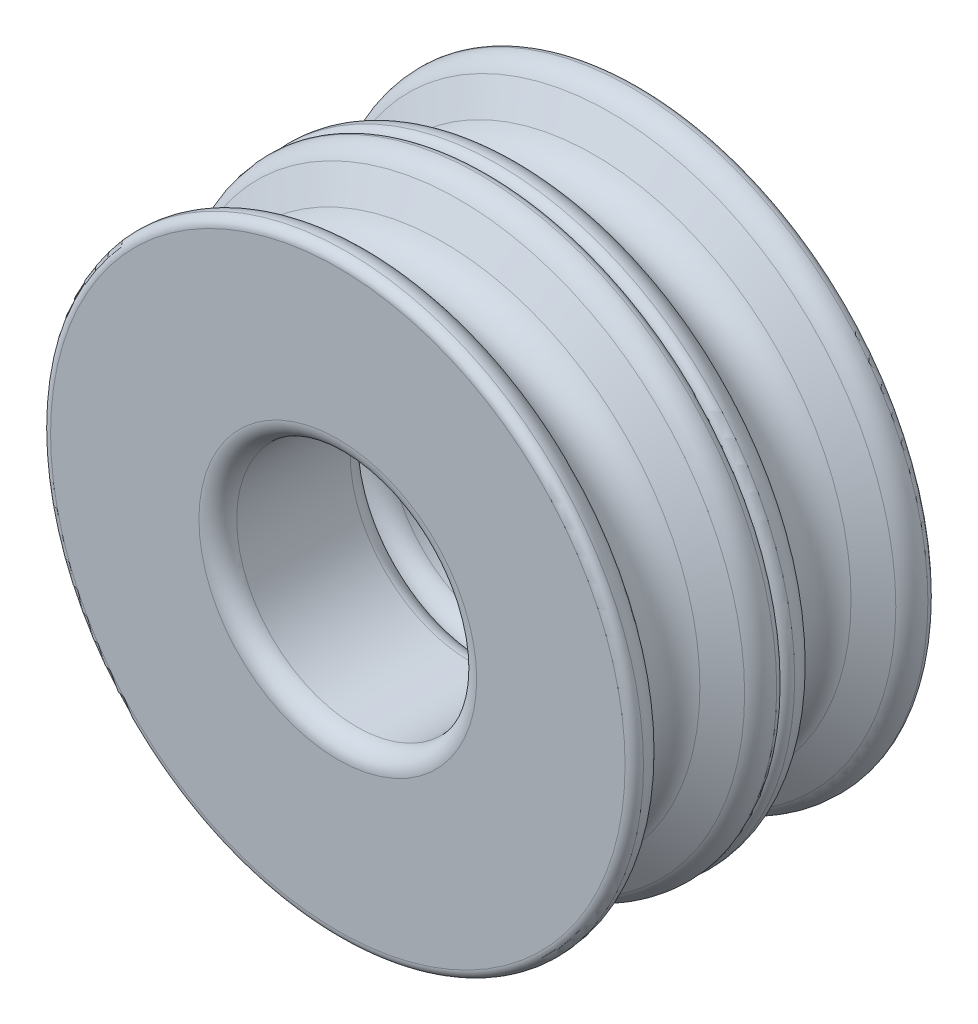
SolidWorks part; units mm, degrees
ref_plane "Front Plane" through (0, 0, 0) normal (0, 0, 1) x (1, 0, 0)
ref_plane "Top Plane" through (0, 0, 0) normal (0, 1, 0) x (1, 0, 0)
ref_plane "Right Plane" through (0, 0, 0) normal (1, 0, 0) x (0, 0, -1)
sketch "Sketch1" plane through (0, 0, 0) normal (1, 0, 0) x (0, 0, -1)
  line L0 (0, 0) -> (0, 17451.5356) construction
  line L2 (-4, 0) -> (-4, 15.2006)
  line L3 (4, 0) -> (4, 15.2006)
  line L6 (-2.4257, 15.1015) -> (-1.5588, 13.6)
  line L7 (2.4257, 15.1015) -> (1.5588, 13.6)
  line L9 (0, 0) -> (-50000, 0) construction
  line L10 (-4, 0) -> (4, 0)
  arc A0 (-4, 15.2006) -> (-3.525, 15.7) centre (-3.5, 15.2006) cw
  arc A1 (4, 15.2006) -> (3.525, 15.7) centre (3.5, 15.2006) ccw
  arc A2 (-3.525, 15.7) -> (-2.4257, 15.1015) centre (-3.465, 14.5015) cw
  arc A3 (3.525, 15.7) -> (2.4257, 15.1015) centre (3.465, 14.5015) ccw
  arc A4 (-1.5588, 13.6) -> (1.5588, 13.6) centre (0, 14.5) ccw
  point P4 (0, 0)
  point P6 (0, 0)
  point P18 (0, 12.7)
  point P20 (0, 0)
  point P21 (-4, 0)
  point P25 (0, 0)
  dimension "D2" = 0.5
  dimension "D4" = 1.2
  dimension "D5" = 1.8
  dimension "D1" = 8
  dimension "D6" = 3
  dimension "D7" = 60
  dimension "D8" = 12.7
revolve "Revolve1" add sketch "Sketch1" angle 360 about L9
sketch "Sketch4" plane through (0, 0, -4) normal (0, 0, -1) x (-1, 0, 0)
  circle A0 centre (0, 0) radius 6.35
  circle A1 centre (0, 0) radius 15.2006
  circle A2 centre (0, 0) radius 15.2006
  dimension "D2" = 12.7
  dimension "D1" = 0
extrude "Cut-Extrude1" cut sketch "Sketch4" against normal blind 10 contours A0
fillet "Fillet1" radius 1 2 edges at (6.35, 0, 4) (-6.35, 0, -4)
ref_plane "Plane1" through (0, 0, 4) normal (0, 0, 1) x (1, 0, 0)
mirror "Mirror1" about plane through (0, 0, 4) normal (0, 0, 1) of bodies 107
